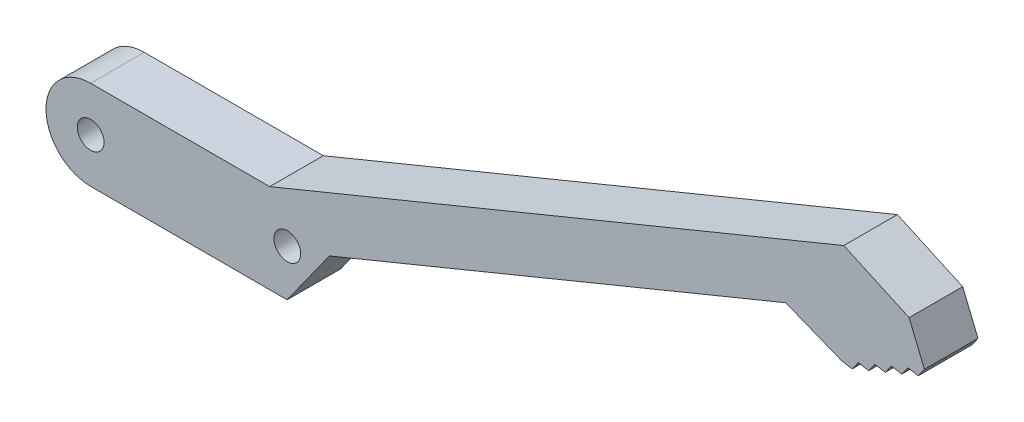
SolidWorks part; units mm, degrees
ref_plane "Front Plane" through (0, 0, 0) normal (0, 0, 1) x (1, 0, 0)
ref_plane "Top Plane" through (0, 0, 0) normal (0, 1, 0) x (1, 0, 0)
ref_plane "Right Plane" through (0, 0, 0) normal (1, 0, 0) x (0, 0, -1)
sketch "Sketch1" plane through (0, 0, 0) normal (0, 0, 1) x (1, 0, 0)
  line L0 (0, 0) -> (22, 0) construction
  line L1 (0, 5) -> (22, 5)
  line L2 (0, -5) -> (22, -5)
  line L3 (20.05, 5) -> (23.9914, -4.5863) construction
  line L4 (20.05, 5) -> (89.4159, 33.5198) construction
  line L5 (23.9914, -4.5863) -> (93.3573, 23.9334) construction
  line L6 (89.4159, 33.5198) -> (93.3573, 23.9334) construction
  line L7 (20.05, 5) -> (84.329, 31.4283)
  line L8 (84.329, 31.4283) -> (91.6461, 28.0954)
  line L9 (91.6461, 28.0954) -> (93.3573, 23.9334)
  line L10 (84.1085, 20.1308) -> (77.8202, 22.6269)
  line L11 (77.8202, 22.6269) -> (26.7299, 1.6211)
  line L12 (84.1085, 20.1308) -> (93.3573, 23.9334) construction
  line L13 (84.1085, 20.1308) -> (85.2729, 19.9284)
  line L14 (85.2729, 19.9284) -> (85.9583, 20.8913)
  line L15 (85.2729, 19.9284) -> (92.672, 22.9705) construction
  line L16 (85.9583, 20.8913) -> (87.1227, 20.6889)
  line L17 (87.1227, 20.6889) -> (87.808, 21.6519)
  line L18 (87.808, 21.6519) -> (88.9725, 21.4495)
  line L19 (88.9725, 21.4495) -> (89.6578, 22.4124)
  line L20 (89.6578, 22.4124) -> (90.8222, 22.21)
  line L21 (90.8222, 22.21) -> (91.5075, 23.1729)
  line L22 (91.5075, 23.1729) -> (92.672, 22.9705)
  line L23 (92.672, 22.9705) -> (93.3573, 23.9334)
  line L24 (26.7299, 1.6211) -> (22, -5)
  arc A0 (0, 5) -> (0, -5) centre (0, 0) ccw
  arc A1 (22, -5) -> (22, 5) centre (22, 0) ccw
  circle A2 centre (0, 0) radius 1.5
  circle A3 centre (22.0207, 0.2068) radius 1.5
  point P3 (11, 0)
  dimension "D11" = 3
  dimension "D1" = 10
  dimension "D2" = 22
  dimension "D3" = 157.65
  dimension "D4" = 1.95
  dimension "D5" = 75
  dimension "D6" = 5.5
  dimension "D7" = 4.5
  dimension "D8" = 10
  dimension "D9" = 136
  dimension "D12" = 2
  dimension "D13" = 0.63
  dimension "D14" = 8
extrude "Boss-Extrude3" add sketch "Sketch1" along normal blind 6 contours A1 L1 A0 L2 A3 A2 | A1 L11 L10 L13 L14 L16 L17 L18 L19 L20 L21 L22 L23 L9 L8 L7 L1
